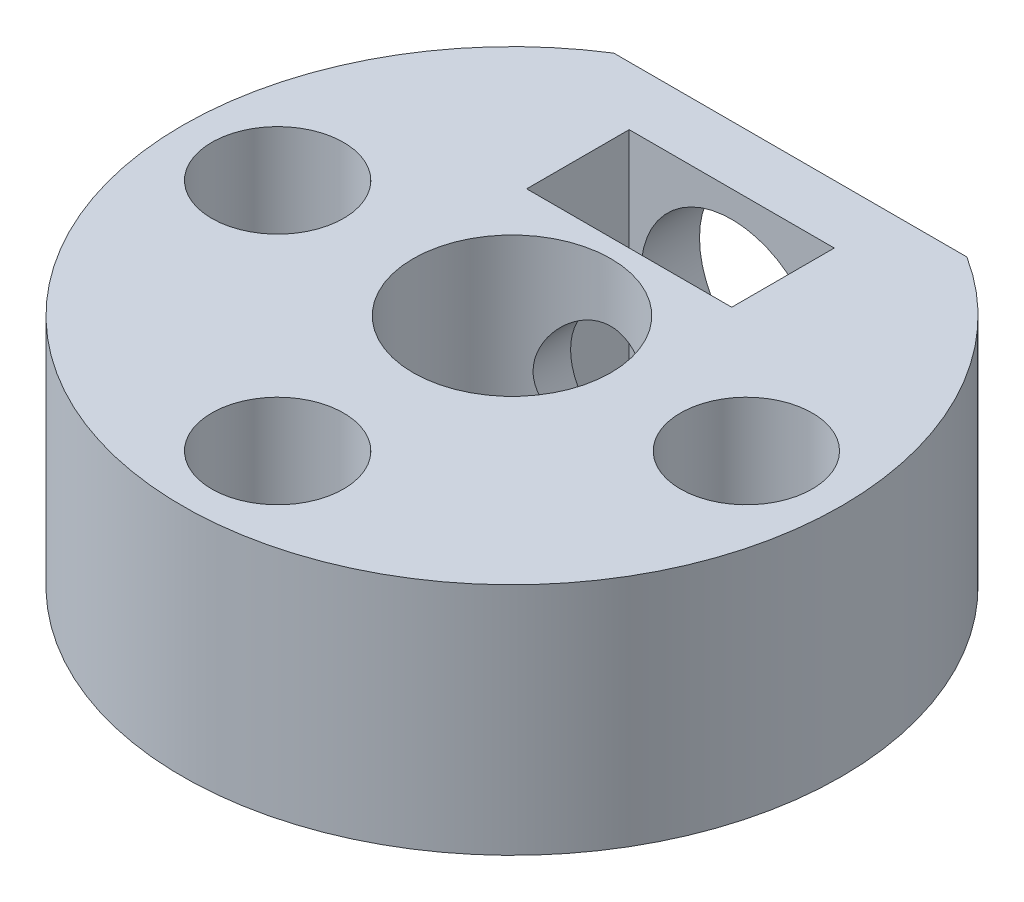
SolidWorks part; units mm, degrees
ref_plane "Plan de face" through (0, 0, 0) normal (0, 0, 1) x (1, 0, 0)
ref_plane "Plan de dessus" through (0, 0, 0) normal (0, 1, 0) x (1, 0, 0)
ref_plane "Plan de droite" through (0, 0, 0) normal (1, 0, 0) x (0, 0, -1)
sketch "Esquisse1" plane through (0, 0, 0) normal (0, 1, 0) x (1, 0, 0)
  line L4 (6.026, 9.5) -> (-6.026, 9.5)
  arc A0 (-6.026, 9.5) -> (6.026, 9.5) centre (0, 0) ccw
  dimension "D1" = 22.5
  dimension "D4" = 9.5
extrude "Boss.-Extru.1" add sketch "Esquisse1" along normal blind 8
sketch "Sketch1" plane through (0, 8, 0) normal (0, 1, 0) x (1, 0, 0)
  circle A0 centre (0, 0) radius 3.375
  dimension "D1" = 6.75
extrude "Cut-Extrude1" cut sketch "Sketch1" against normal through all
sketch "Esquisse7" plane through (0, 8, 0) normal (0, 1, 0) x (1, 0, 0)
  line L1 (-3.5, 4) -> (3.5, 4)
  line L2 (-3.5, 4) -> (-3.5, 7.5)
  line L3 (-3.5, 7.5) -> (3.5, 7.5)
  line L4 (3.5, 4) -> (3.5, 7.5)
  line L5 (-3.5, 4) -> (3.5, 7.5) construction
  line L6 (-3.5, 7.5) -> (3.5, 4) construction
  point P0 (0, 5.75)
  dimension "D3" = 4
  dimension "D1" = 3.5
  dimension "D2" = 7
extrude "Enlèv. mat.-Extru.2" cut sketch "Esquisse7" against normal through all
sketch "Esquisse8" plane through (0, 0, 0) normal (0, -1, 0) x (1, 0, 0)
  line L0 (-6.026, -9.5) -> (6.026, -9.5)
  line L1 (6.026, -9.5) -> (-6.026, -9.5) construction
  arc A0 (6.026, -9.5) -> (-6.026, -9.5) centre (0, 0) ccw
extrude "Boss.-Extru.2" [suppressed] add sketch "Esquisse8" along normal blind 3
hole_wizard "Chambrage pour vis à tête cylindrique à 6 pans creux (ou vis CHC) M21" positions "Esquisse12" profile "Esquisse13" counterbore size "M2" standard "Ansi Metric" end condition through all
sketch "Esquisse12" plane through (0, 8, 0) normal (0, 1, 0) x (1, 0, 0)
  line L0 (-8, 0) -> (0, 0) construction
  line L1 (0, 0) -> (0, -8) construction
  line L3 (0, 0) -> (8, 0) construction
  point P0 (-8, 0)
  point P2 (0, -8)
  point P4 (8, 0)
  dimension "D1" = 8
sketch "Esquisse13" plane through (-8, 8, 0) normal (1, 0, 0) x (0, 0, 1)
  line L0 (0, 0) -> (0, 8)
  line L1 (0, 8) -> (1.25, 8)
  line L3 (1.25, 8) -> (1.25, 5.3)
  line L4 (1.25, 5.3) -> (2.25, 5.3)
  line L5 (2.25, 5.3) -> (2.25, 0)
  line L7 (2.25, 0) -> (0, 0)
  line L11 (0, -6.35) -> (0, 107.95) construction
  dimension "Diamètre du perçage jusqu'au prochain" = 2.5
  dimension "Profondeur du perçage jusqu'au prochain" = 8
  dimension "Diamètre du chambrage" = 4.5
  dimension "Profondeur du chambrage" = 5.3
sketch "Esquisse14" [suppressed] plane through (0, -3, 0) normal (0, -1, 0) x (1, 0, 0)
  circle A0 centre (0, 0) radius 4.25
  dimension "D1" = 8.5
extrude "Enlèv. mat.-Extru.3" [suppressed] cut sketch "Esquisse14" against normal blind 2
hole_wizard "CBORE for M5 Hex Head Bolt1" positions "Sketch2" profile "Sketch3" counterbore size "M5" standard "ANSI Metric"
sketch "Sketch2" plane through (0, 0, -9.5) normal (0, 0, -1) x (-1, 0, 0)
  point P0 (0, 4)
  dimension "D1" = 4
sketch "Sketch3" plane through (0, 4, -9.5) normal (1, 0, 0) x (0, 1, 0)
  line L0 (0, 0) -> (0, 10.7007)
  line L1 (0, 10.7007) -> (2, 9.499)
  line L2 (2, 9.499) -> (2, 2)
  line L3 (2, 2) -> (3.1, 2)
  line L4 (3.1, 2) -> (3.1, 0)
  line L5 (3.1, 0) -> (0, 0)
  line L10 (0, 10.7007) -> (-2, 9.499) construction
  line L11 (0, -6.35) -> (0, 107.95) construction
  dimension "Hole Dia." = 4
  dimension "Hole Depth" = 9.499
  dimension "C'Bore Dia." = 6.2
  dimension "C'Bore Depth" = 2
  dimension "Drill Angle" = 118
